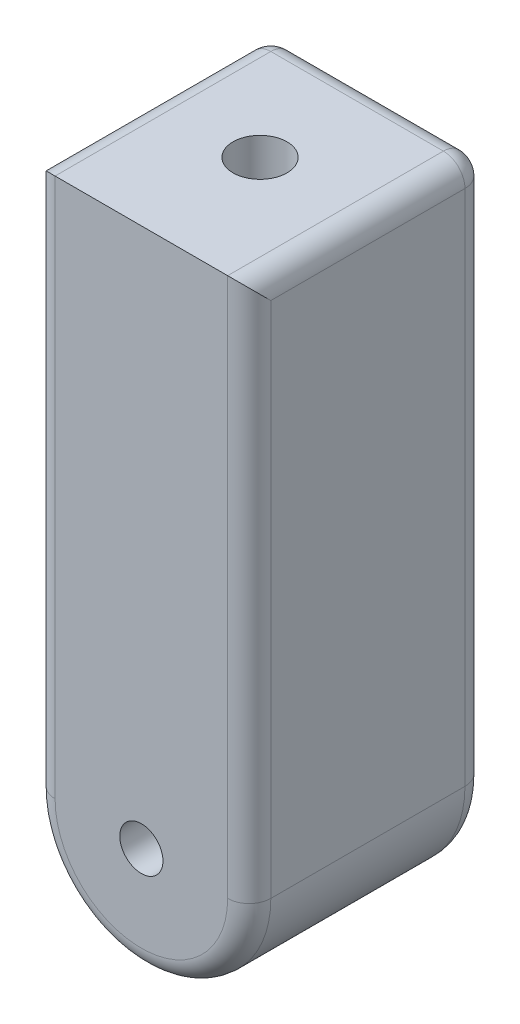
SolidWorks part; units mm, degrees
ref_plane "Front Plane" through (0, 0, 0) normal (0, 0, 1) x (1, 0, 0)
ref_plane "Top Plane" through (0, 0, 0) normal (0, 1, 0) x (1, 0, 0)
ref_plane "Right Plane" through (0, 0, 0) normal (1, 0, 0) x (0, 0, -1)
sketch "Sketch2" plane through (0, 0, 0) normal (0, 0, 1) x (1, 0, 0)
  line L0 (-50, -100) -> (-50, -150)
  line L1 (-50, 100) -> (50, 100)
  line L2 (-50, 100) -> (-50, -100)
  line L3 (-50, -100) -> (50, -100)
  line L4 (50, 100) -> (50, -100)
  line L5 (-50, 100) -> (50, -100) construction
  line L6 (-50, -100) -> (50, 100) construction
  line L7 (50, -100) -> (50, -150)
  arc A0 (50, -150) -> (-50, -150) centre (0, -150) cw
  point P0 (0, 0)
  dimension "D1" = 100
  dimension "D2" = 200
  dimension "D3" = 50
  dimension "D4" = 50
extrude "Boss-Extrude1" add sketch "Sketch2" along normal mid plane 110 contours L4 L1 L2 L3 | A0 L7 L3 L0
sketch "Sketch3" plane through (0, 0, 55) normal (0, 0, 1) x (1, 0, 0)
  circle A0 centre (0, -150) radius 10
  dimension "D1" = 20
extrude "Cut-Extrude1" cut sketch "Sketch3" against normal up to surface (110 mm away) up to face at (0, -37.5, -55)
sketch "Sketch4" plane through (0, 100, 0) normal (0, 1, 0) x (1, 0, 0)
  circle A0 centre (0, 0) radius 12.5
  dimension "D1" = 25
extrude "Cut-Extrude2" cut sketch "Sketch4" against normal blind 100
fillet "Fillet1" radius 10 10 edges at (-50, -25, 55) (0, -200, 55) (0, 100, -55) (-50, -25, -55) (0, -200, -55) (50, -25, -55) (10, -150, -55) (-50, 100, 0) (50, 100, 0) (50, -25, 55)
